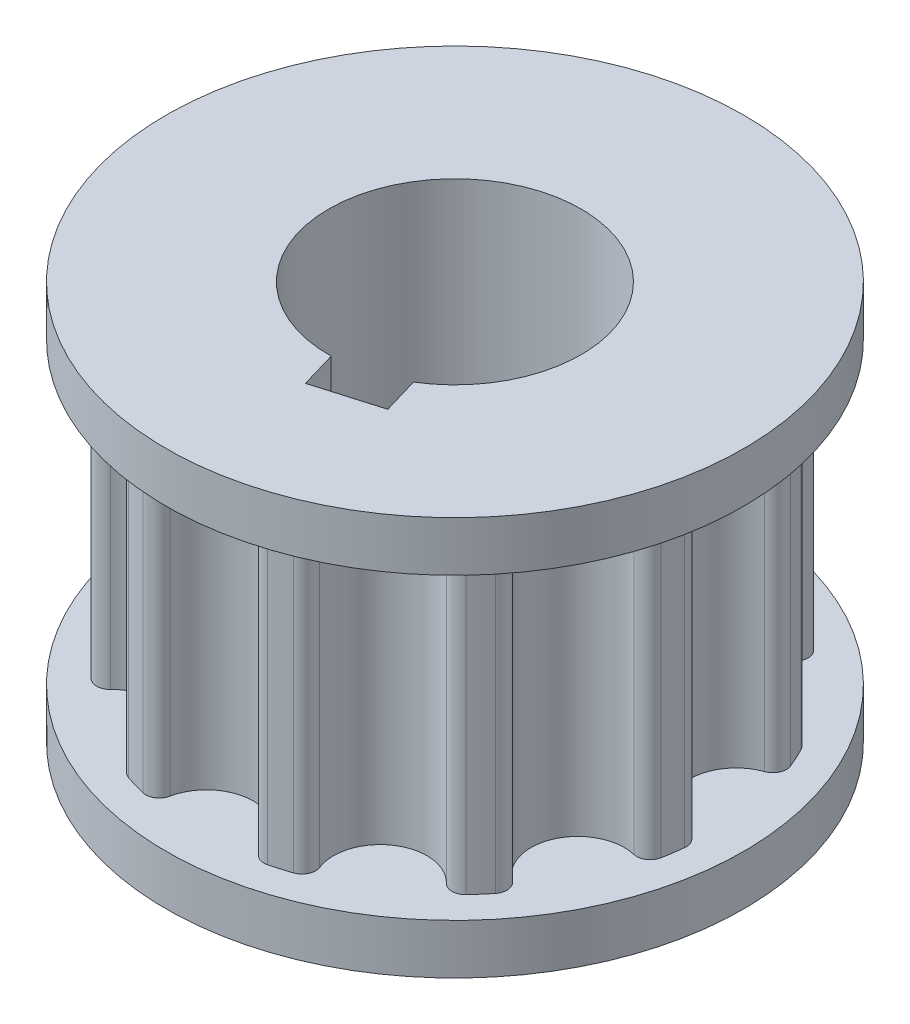
SolidWorks part; units mm, degrees
ref_plane "Front Plane" through (0, 0, 0) normal (0, 0, 1) x (1, 0, 0)
ref_plane "Top Plane" through (0, 0, 0) normal (0, 1, 0) x (1, 0, 0)
ref_plane "Right Plane" through (0, 0, 0) normal (1, 0, 0) x (0, 0, -1)
sketch "Sketch1" plane through (0, 0, 0) normal (0, 0, 1) x (1, 0, 0)
  line L0 (9.182, 1.5875) -> (0, 1.5875)
  line L1 (0, 1.5875) -> (0, 0)
  line L2 (0, 0) -> (9.182, 0)
  line L3 (9.182, 0) -> (9.182, 1.5875)
  line L4 (0, 1.5875) -> (0, 0) construction
revolve "Revolve1" add sketch "Sketch1" angle 360 about L4
sketch "Sketch2" plane through (0, 0, 0) normal (0, -1, 0) x (1, 0, 0)
  arc A0 (7.0507, -4.1512) -> (5.1124, -6.3882) centre (5.9676, -5.171) ccw
  arc A1 (5.1124, -6.3882) -> (3.6871, -7.3041) centre (0, 0) cw
  arc A2 (3.6871, -7.3041) -> (0.8471, -8.1381) centre (2.2246, -7.5764) ccw
  arc A3 (0.8471, -8.1381) -> (-0.8471, -8.1381) centre (0, 0) cw
  arc A4 (-0.8471, -8.1381) -> (-3.6871, -7.3041) centre (-2.2246, -7.5764) ccw
  arc A5 (-3.6871, -7.3041) -> (-5.1124, -6.3882) centre (0, 0) cw
  arc A6 (-5.1124, -6.3882) -> (-7.0507, -4.1512) centre (-5.9676, -5.171) ccw
  arc A7 (-7.0507, -4.1512) -> (-7.7545, -2.6101) centre (0, 0) cw
  arc A8 (-7.7545, -2.6101) -> (-8.1758, 0.3197) centre (-7.8159, -1.1238) ccw
  arc A9 (-8.1758, 0.3197) -> (-7.9347, 1.9966) centre (0, 0) cw
  arc A10 (-7.9347, 1.9966) -> (-6.7051, 4.6891) centre (-7.1827, 3.2802) ccw
  arc A11 (-6.7051, 4.6891) -> (-5.5956, 5.9695) centre (0, 0) cw
  arc A12 (-5.5956, 5.9695) -> (-3.1055, 7.5698) centre (-4.269, 6.6428) ccw
  arc A13 (-3.1055, 7.5698) -> (-1.48, 8.0471) centre (0, 0) cw
  arc A14 (-1.48, 8.0471) -> (1.48, 8.0471) centre (0, 7.8963) ccw
  arc A15 (1.48, 8.0471) -> (3.1055, 7.5698) centre (0, 0) cw
  arc A16 (3.1055, 7.5698) -> (5.5956, 5.9695) centre (4.269, 6.6428) ccw
  arc A17 (5.5956, 5.9695) -> (6.7051, 4.6891) centre (0, 0) cw
  arc A18 (6.7051, 4.6891) -> (7.9347, 1.9966) centre (7.1827, 3.2802) ccw
  arc A19 (7.9347, 1.9966) -> (8.1758, 0.3197) centre (0, 0) cw
  arc A20 (8.1758, 0.3197) -> (7.7545, -2.6101) centre (7.8159, -1.1238) ccw
  arc A21 (7.7545, -2.6101) -> (7.0507, -4.1512) centre (0, 0) cw
extrude "Boss-Extrude1" add sketch "Sketch2" along normal blind 9.5
ref_plane "Plane1" through (0, -9.5, 0) normal (0, 1, 0) x (1, 0, 0)
sketch "Sketch3" plane through (0, -9.5, 0) normal (0, 1, 0) x (1, 0, 0)
  circle A0 centre (0, 0) radius 9.182
extrude "Boss-Extrude2" add sketch "Sketch3" against normal blind 1.5875
sketch "Sketch4" plane through (0, -11.0875, 0) normal (0, -1, 0) x (1, 0, 0)
  line L0 (2.4426, 4.5773) -> (0.4198, 5.1712)
  line L1 (0.4198, 5.1712) -> (0.0795, 4.0124)
  line L2 (2.1024, 3.4185) -> (2.4426, 4.5773)
  arc A0 (0.0795, 4.0124) -> (2.1024, 3.4185) centre (0, 0) cw
extrude "Cut-Extrude1" cut sketch "Sketch4" against normal through all
ref_plane "Plane2" through (0, 0, 0) normal (0, 0, -1) x (-1, 0, 0)
sketch "Sketch5" plane through (0, 0, 0) normal (0, 0, -1) x (-1, 0, 0)
  line L0 (-4.0132, -20.0875) -> (0, -20.0875)
  line L1 (0, -20.0875) -> (0, 1.5875)
  line L2 (0, 1.5875) -> (-4.0132, 1.5875)
  line L3 (-4.0132, 1.5875) -> (-4.0132, -20.0875)
  line L4 (0, -20.0875) -> (0, 1.5875) construction
revolve "Cut-Revolve1" cut sketch "Sketch5" angle 360 about L4
fillet "Fillet1" radius 0.43 22 edges at (-5.1124, -4.75, -6.3882) (3.6871, -4.75, -7.3041) (-7.9347, -4.75, 1.9966) (1.48, -4.75, 8.0471) (-0.8471, -4.75, -8.1381) (5.5956, -4.75, 5.9695) (-7.7545, -4.75, -2.6101) (3.1055, -4.75, 7.5698) (-5.5956, -4.75, 5.9695) (7.9347, -4.75, 1.9966) (-3.6871, -4.75, -7.3041) (6.7051, -4.75, 4.6891) (-7.0507, -4.75, -4.1512) (7.7545, -4.75, -2.6101) (-8.1758, -4.75, 0.3197) (8.1758, -4.75, 0.3197) (-6.7051, -4.75, 4.6891) (5.1124, -4.75, -6.3882) (-3.1055, -4.75, 7.5698) (7.0507, -4.75, -4.1512) (-1.48, -4.75, 8.0471) (0.8471, -4.75, -8.1381)
